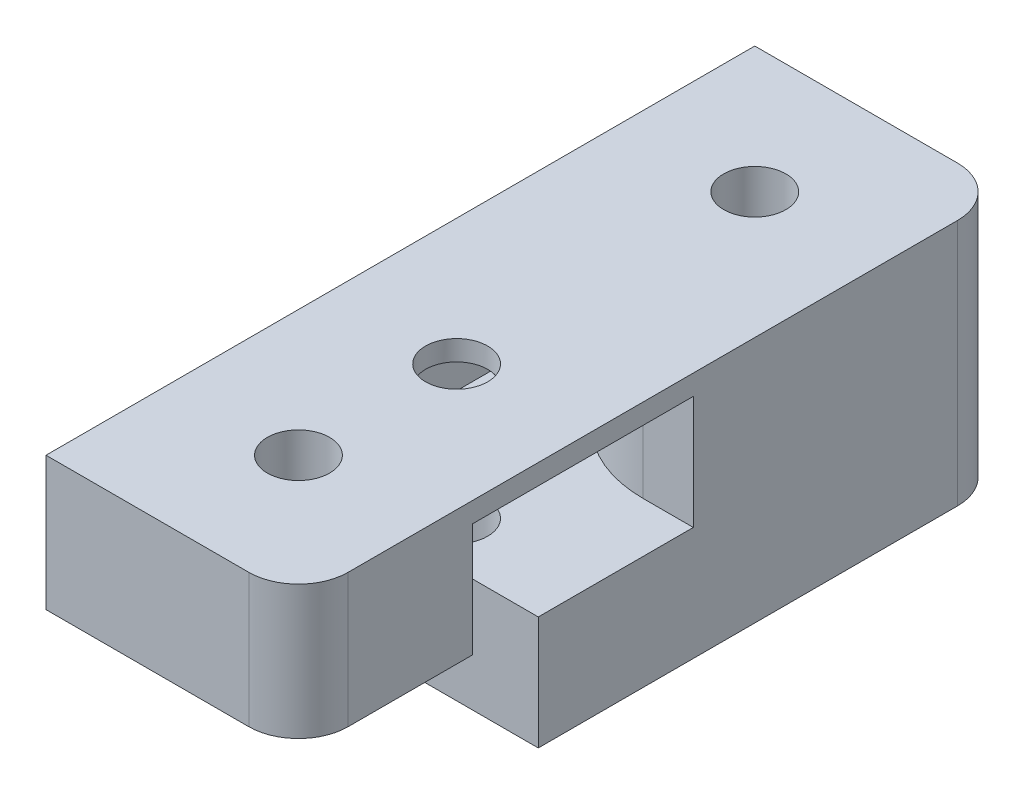
SolidWorks part; units mm, degrees
ref_plane "Front Plane" through (0, 0, 0) normal (0, 0, 1) x (1, 0, 0)
ref_plane "Top Plane" through (0, 0, 0) normal (0, 1, 0) x (1, 0, 0)
ref_plane "Right Plane" through (0, 0, 0) normal (1, 0, 0) x (0, 0, -1)
sketch "Sketch1" plane through (0, 0, 0) normal (0, 1, 0) x (1, 0, 0)
  line L0 (0, 0) -> (0, 36.73) construction
  line L2 (-10.16, -10.16) -> (10.16, -10.16)
  line L3 (-10.16, -10.16) -> (-10.16, 46.89)
  line L4 (-10.16, 46.89) -> (10.16, 46.89)
  line L5 (10.16, -10.16) -> (10.16, 46.89)
  line L6 (-10.16, -10.16) -> (10.16, 46.89) construction
  line L7 (-10.16, 46.89) -> (10.16, -10.16) construction
  circle A0 centre (0, 0) radius 2.5
  circle A1 centre (0, 36.73) radius 2.5
  point P5 (0, 18.365)
  dimension "D4" = 5
  dimension "D1" = 36.73
  dimension "D2" = 20.32
  dimension "D3" = 57.05
extrude "Boss-Extrude1" add sketch "Sketch1" along normal blind 19.9
fillet "Fillet1" radius 4 2 edges at (10.16, 9.95, -46.89) (10.16, 9.95, 10.16)
sketch "Sketch2" plane through (0, 0, 0) normal (0, -1, 0) x (1, 0, 0)
  line L0 (-1.016, -9.144) -> (10.16, -9.144)
  line L1 (10.16, 6.16) -> (10.16, -42.89) construction
  line L2 (10.16, -9.144) -> (10.16, 10.16)
  line L3 (10.16, 10.16) -> (-10.16, 10.16)
  line L4 (-10.16, 10.16) -> (6.16, 10.16) construction
  line L5 (-10.16, 10.16) -> (-10.16, 0)
  line L7 (-10.16, -46.89) -> (-10.16, 10.16) construction
  line L8 (0, 0) -> (-1.016, 0) construction
  arc A0 (-10.16, 0) -> (-1.016, -9.144) centre (-1.016, 0) ccw
  dimension "D1" = 9.144
extrude "Cut-Extrude1" cut sketch "Sketch2" against normal blind 9.136
sketch "Sketch3" plane through (0, 19.9, 0) normal (0, 1, 0) x (1, 0, 0)
  circle A0 centre (0, 12.73) radius 2.5
  circle A1 centre (0, 0) radius 2.5 construction
  point P2 (0, 0)
  point P6 (3.8558, 12.132)
  dimension "D1" = 12.73
extrude "Cut-Extrude2" cut sketch "Sketch3" against normal through all
sketch "Sketch4" plane through (0, 19.9, 0) normal (0, 1, 0) x (1, 0, 0)
  line L0 (0, 3.84) -> (10.16, 3.84)
  line L1 (10.16, -6.16) -> (10.16, 42.89) construction
  line L2 (10.16, 3.84) -> (10.16, 21.62)
  line L3 (-3.89, 46.89) -> (-8.89, 46.89)
  line L4 (-8.89, 46.89) -> (-8.89, 12.73)
  line L5 (6.16, 46.89) -> (-10.16, 46.89) construction
  line L6 (10.16, 21.62) -> (6.11, 21.62)
  line L7 (-3.89, 31.62) -> (-3.89, 46.89)
  arc A0 (-8.89, 12.73) -> (0, 3.84) centre (0, 12.73) ccw
  circle A1 centre (0, 12.73) radius 2.5 construction
  arc A2 (6.11, 21.62) -> (-3.89, 31.62) centre (6.11, 31.62) cw
  dimension "D1" = 8.89
  dimension "D4" = 10
  dimension "D2" = 5
  dimension "D3" = 17.78
extrude "Cut-Extrude3" cut sketch "Sketch4" along normal blind 9.136 from surface at -10.764 starting at face at (0, 9.136, -2.5)
fillet "Fillet2" radius 1 1 edges at (-10.16, 4.568, 0)
